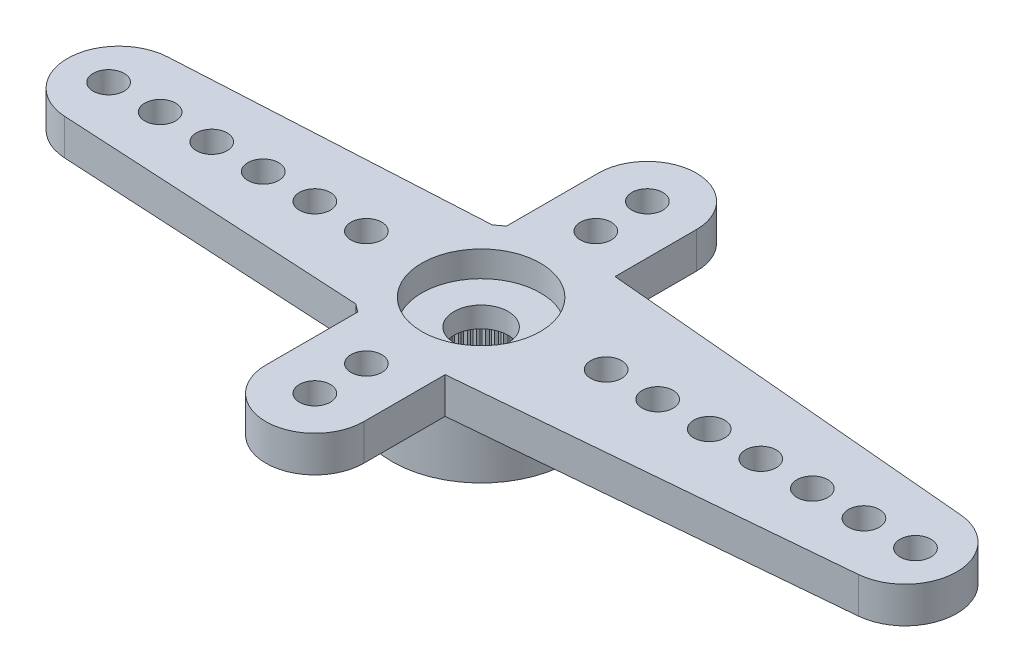
SolidWorks part; units mm, degrees
material "PVC Rígido"
ref_plane "Plano frontal" through (0, 0, 0) normal (0, 0, 1) x (1, 0, 0)
ref_plane "Plano superior" through (0, 0, 0) normal (0, 1, 0) x (1, 0, 0)
ref_plane "Plano direito" through (0, 0, 0) normal (1, 0, 0) x (0, 0, -1)
sketch "Esboço1" plane through (0, 0, 0) normal (0, 1, 0) x (1, 0, 0)
  line L0 (0, 0) -> (-14.05, 0) construction
  line L1 (-14.1591, 1.997) -> (-2.2091, 2.65)
  line L2 (-2.2091, -2.65) -> (-14.1591, -1.997)
  arc A0 (-2.2091, -2.65) -> (-2.2091, 2.65) centre (0, 0) ccw
  arc A1 (-14.1591, 1.997) -> (-14.1591, -1.997) centre (-14.05, 0) ccw
  dimension "D1" = 6.9
  dimension "D2" = 4
  dimension "D3" = 19.5
  dimension "D4" = 5.3
extrude "Ressalto-extrusão1" add sketch "Esboço1" against normal blind 1.4
sketch "Esboço2" plane through (0, -1.4, 0) normal (0, -1, 0) x (1, 0, 0)
  arc A0 (-2.2091, -2.65) -> (-2.2091, 2.65) centre (0, 0) ccw construction
  circle A1 centre (0, 0) radius 3.45
extrude "Ressalto-extrusão2" add sketch "Esboço2" along normal offset from surface (2.4 mm away) 3.8 up to face at (-7.242, 0, 0)
hole_wizard "Furo1" positions "Esboço9" profile "Esboço10" legacy end condition through all
sketch "Esboço9" plane through (0, 0, 0) normal (0, 1, 0) x (1, 0, 0)
  line L1 (-14.45, 0) -> (0, 0) construction
  arc A2 (-14.1591, 1.997) -> (-14.1591, -1.997) centre (-14.05, 0) ccw construction
  point P0 (-14.45, 0)
  point P19 (-16.05, 0)
  dimension "D1" = 1.6
sketch "Esboço10" plane through (-14.45, 0, 0) normal (1, 0, 0) x (0, 0, 1)
  line L0 (0, 0) -> (0, 3.8)
  line L1 (0, 3.8) -> (0.6, 3.8)
  line L2 (0.6, 3.8) -> (0.6, 0)
  line L3 (0.6, 0) -> (0, 0)
  line L4 (0, 110) -> (0, -10) construction
  dimension "Diameter" = 1.2
  dimension "Depth" = 3.8
pattern_linear "Padrão linear1" count 6 spacing 2 along (1, 0, 0) of "Furo1"
sketch "Esboço12" plane through (0, 0, 0) normal (0, 1, 0) x (1, 0, 0)
  line L0 (0.3041, 3.4366) -> (16.6263, 1.9922)
  line L1 (16.6263, -1.9922) -> (0.3041, -3.4366)
  arc A0 (-2.2091, -2.65) -> (-2.2091, 2.65) centre (0, 0) ccw construction
  arc A1 (0.3041, -3.4366) -> (0.3041, 3.4366) centre (0, 0) ccw
  arc A2 (16.6263, 1.9922) -> (16.6263, -1.9922) centre (16.45, 0) cw
  arc A3 (-14.1591, 1.997) -> (-14.1591, -1.997) centre (-14.05, 0) ccw construction
  dimension "D1" = 2
  dimension "D2" = 34.5
extrude "Ressalto-extrusão3" add sketch "Esboço12" against normal up to surface (1.4 mm away) up to face at (-12.45, -1.4, 0.6)
hole_wizard "Furo2" positions "Esboço13" profile "Esboço14" legacy end condition through all
sketch "Esboço13" plane through (0, 0, 0) normal (0, 1, 0) x (1, 0, 0)
  line L0 (0, 0) -> (16.85, 0) construction
  arc A0 (16.6263, -1.9922) -> (16.6263, 1.9922) centre (16.45, 0) ccw construction
  point P0 (16.85, 0)
  point P6 (18.45, 0)
  dimension "D1" = 1.6
sketch "Esboço14" plane through (16.85, 0, 0) normal (1, 0, 0) x (0, 0, 1)
  line L0 (0, 0) -> (0, 3.8)
  line L1 (0, 3.8) -> (0.6, 3.8)
  line L2 (0.6, 3.8) -> (0.6, 0)
  line L3 (0.6, 0) -> (0, 0)
  line L4 (0, 110) -> (0, -10) construction
  dimension "Diameter" = 1.2
  dimension "Depth" = 3.8
pattern_linear "Padrão linear2" count 7 spacing 2 along (-1, 0, 0) of "Furo2"
sketch "Esboço16" plane through (0, 0, 0) normal (0, 1, 0) x (1, 0, 0)
  line L0 (0, -6.45) -> (0, 6.45) construction
  line L1 (-1.9, -6.45) -> (-1.9, 6.45)
  line L2 (1.9, -6.45) -> (1.9, 6.45)
  arc A0 (-1.9, -6.45) -> (1.9, -6.45) centre (0, -6.45) ccw
  arc A1 (1.9, 6.45) -> (-1.9, 6.45) centre (0, 6.45) ccw
  point P2 (0, 0)
  dimension "D2" = 16.7
  dimension "D1" = 3.8
extrude "Ressalto-extrusão4" add sketch "Esboço16" against normal up to surface (1.4 mm away) up to face at (14.85, -1.4, 0.6)
hole_wizard "Furo3" positions "Esboço17" profile "Esboço18" legacy end condition through all
sketch "Esboço17" plane through (0, 0, 0) normal (0, 1, 0) x (1, 0, 0)
  point P0 (0, -6.45)
sketch "Esboço18" plane through (0, 0, 6.45) normal (1, 0, 0) x (0, 0, 1)
  line L0 (0, 0) -> (0, 3.8)
  line L1 (0, 3.8) -> (0.6, 3.8)
  line L2 (0.6, 3.8) -> (0.6, 0)
  line L3 (0.6, 0) -> (0, 0)
  line L4 (0, 110) -> (0, -10) construction
  dimension "Diameter" = 1.2
  dimension "Depth" = 3.8
pattern_linear "Padrão linear3" count 2 spacing 2 along (0, 0, -1) of "Furo3"
pattern_circular "PadrãoCircular1" count 2 over 360 about axis through (0, 0, 0) along (0, 1, 0) of "Padrão linear3", "Furo3"
hole_wizard "Furo4" positions "Esboço3" profile "Esboço4" legacy
sketch "Esboço3" plane through (0, -3.8, 0) normal (0, -1, 0) x (-1, 0, 0)
  point P0 (0, 0)
sketch "Esboço4" plane through (0, -3.8, 0) normal (1, 0, 0) x (0, 0, -1)
  line L0 (0, 0) -> (0, 2)
  line L1 (0, 2) -> (2.475, 2)
  line L2 (2.475, 2) -> (2.475, 0)
  line L3 (2.475, 0) -> (0, 0)
  line L4 (0, 110) -> (0, -10) construction
  dimension "Diameter" = 4.95
  dimension "Depth" = 2
hole_wizard "Furo5" positions "Esboço5" profile "Esboço6" legacy
sketch "Esboço5" plane through (0, 0, 0) normal (0, 1, 0) x (1, 0, 0)
  point P0 (0, 0)
sketch "Esboço6" plane through (0, 0, 0) normal (1, 0, 0) x (0, 0, 1)
  line L0 (0, 0) -> (0, 1)
  line L1 (0, 1) -> (2.3, 1)
  line L2 (2.3, 1) -> (2.3, 0)
  line L3 (2.3, 0) -> (0, 0)
  line L4 (0, 110) -> (0, -10) construction
  dimension "Diameter" = 4.6
  dimension "Depth" = 1
hole_wizard "Furo6" positions "Esboço7" profile "Esboço8" legacy end condition through all
sketch "Esboço7" plane through (0, 0, 0) normal (0, 1, 0) x (1, 0, 0)
  point P0 (0, 0)
sketch "Esboço8" plane through (0, 0, 0) normal (1, 0, 0) x (0, 0, 1)
  line L0 (0, 0) -> (0, 3.8)
  line L1 (0, 3.8) -> (1.05, 3.8)
  line L2 (1.05, 3.8) -> (1.05, 0)
  line L3 (1.05, 0) -> (0, 0)
  line L4 (0, 110) -> (0, -10) construction
  dimension "Diameter" = 2.1
  dimension "Depth" = 3.8
sketch "Esboço11" plane through (0, -3.8, 0) normal (0, -1, 0) x (1, 0, 0)
  line L0 (-0.0981, 2.4731) -> (0, 2.375)
  line L1 (0, 2.375) -> (0.0981, 2.4731)
  line L2 (0, 0) -> (0, 2.475) construction
  circle A0 centre (0, 0) radius 2.375 construction
  circle A1 centre (0, 0) radius 2.475
  arc A2 (0.0981, 2.4731) -> (-0.0981, 2.4731) centre (0, 0) ccw
  dimension "D3" = 4.75
  dimension "D2" = 0.1
  dimension "D1" = 0
extrude "Ressalto-extrusão5" add sketch "Esboço11" against normal up to surface (2 mm away) up to face at (0, -1.8, 1.05)
pattern_circular "PadrãoCircular2" count 60 over 360 about axis through (0, 0, 0) along (0, 1, 0) of "Ressalto-extrusão5"
sketch "Çizim1" plane through (0, -1, 0) normal (0, 1, 0) x (1, 0, 0)
